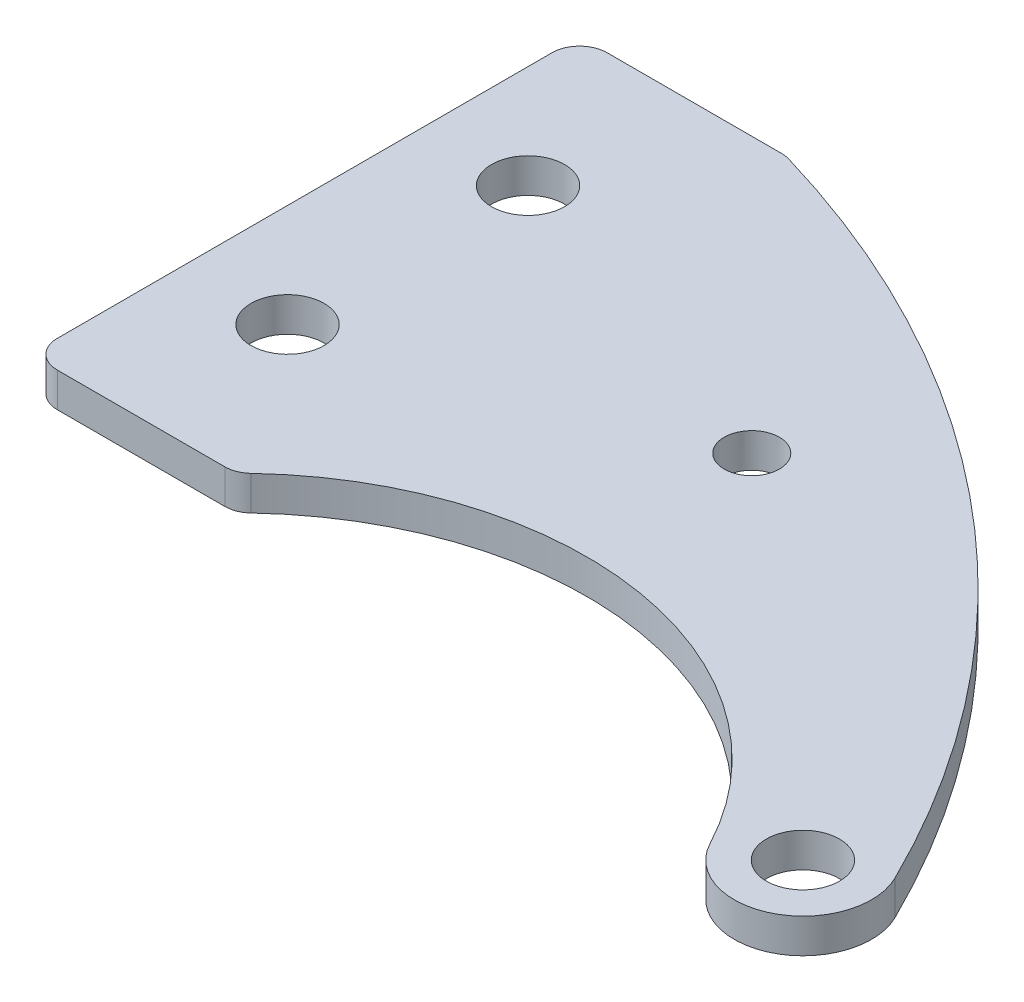
SolidWorks part; units mm, degrees
material "6061-T6 (SS)"
ref_plane "Front" through (0, 0, 0) normal (0, 0, 1) x (1, 0, 0)
ref_plane "Top" through (0, 0, 0) normal (0, 1, 0) x (1, 0, 0)
ref_plane "Right" through (0, 0, 0) normal (1, 0, 0) x (0, 0, -1)
sketch "Sketch1" plane through (0, 0, 0) normal (0, 1, 0) x (1, 0, 0)
  line L1 (0, 50.8) -> (19.05, 50.8)
  line L4 (0, 50.8) -> (0, 0)
  line L6 (0, 0) -> (19.05, 0)
  arc A0 (81.8992, -1.9621) -> (70.584, -7.7262) centre (76.2, -4.7625) cw
  arc A3 (19.05, 0) -> (70.584, -7.7262) centre (41.9743, -22.8241) cw
  arc A6 (81.8992, -1.9621) -> (19.05, 50.8) centre (-9.2873, -46.7682) ccw
  dimension "D1" = 19.05
  dimension "D2" = 4.7625
  dimension "D3" = 6.35
  dimension "D4" = 76.2
  dimension "D6" = 9.525
  dimension "D7" = 101.6
  dimension "D5" = 50.8
extrude "Boss-Extrude1" add sketch "Sketch1" along normal blind 3.175
hole_wizard "1/4 Clearance Hole2" positions "Sketch4" profile "Sketch3" hole size "1/4" standard "ANSI Inch" end condition through all
sketch "Sketch4" plane through (0, 0, 0) normal (0, -1, 0) x (-1, 0, 0)
  point P0 (-76.2, -4.7625)
sketch "Sketch3" plane through (76.2, 0, 4.7625) normal (1, 0, 0) x (0, 0, -1)
  line L0 (0, 0) -> (0, 3.175)
  line L1 (0, 3.175) -> (3.3782, 3.175)
  line L2 (3.3782, 3.175) -> (3.3782, 0)
  line L5 (3.3782, 0) -> (0, 0)
  line L11 (0, -6.35) -> (0, 107.95) construction
  dimension "Thru Hole Dia." = 6.7564
  dimension "Thru Hole Depth" = 3.175
hole_wizard "1/4 Clearance Hole1" positions "Sketch7" profile "Sketch8" hole size "1/4" standard "ANSI Inch" end condition through all
sketch "Sketch7" plane through (0, 3.175, 0) normal (0, 1, 0) x (1, 0, 0)
  line L9 (9.525, 0) -> (9.525, 14.2875) construction
  line L10 (0, 0) -> (19.05, 0) construction
  line L11 (9.525, 14.2875) -> (9.525, 36.5125) construction
  line L12 (9.525, 36.5125) -> (9.525, 50.8) construction
  line L13 (19.05, 50.8) -> (0, 50.8) construction
  point P0 (9.525, 36.5125)
  point P2 (9.525, 14.2875)
  dimension "D1" = 22.225
sketch "Sketch8" plane through (9.525, 3.175, -36.5125) normal (1, 0, 0) x (0, 0, 1)
  line L0 (0, 0) -> (0, 3.175)
  line L1 (0, 3.175) -> (3.3782, 3.175)
  line L2 (3.3782, 3.175) -> (3.3782, 0)
  line L5 (3.3782, 0) -> (0, 0)
  line L11 (0, -6.35) -> (0, 107.95) construction
  dimension "Thru Hole Dia." = 6.7564
  dimension "Thru Hole Depth" = 3.175
fillet "Fillet1" radius 2.54 4 edges at (19.05, 1.5875, 0) (0, 1.5875, 0) (0, 1.5875, -50.8) (19.05, 1.5875, -50.8)
sketch "Sketch11" plane through (0, 3.175, 0) normal (0, 1, 0) x (1, 0, 0)
  line L0 (41.275, 41.3568) -> (41.275, 9.5174) construction
  circle A0 centre (9.525, 36.5125) radius 3.3782 construction
  arc A1 (81.8992, -1.9621) -> (19.4036, 50.6966) centre (-9.2873, -46.7682) ccw construction
  arc A2 (70.584, -7.7262) -> (19.762, 0.6934) centre (41.9743, -22.8241) ccw construction
  point P0 (41.275, 25.4371)
  point P14 (0, 0)
  dimension "D1" = 31.75
hole_wizard "#10 Clearance Hole1" positions "Sketch11" profile "Sketch10" hole size "#10" standard "ANSI Inch" end condition up to next
sketch "Sketch10" plane through (41.275, 3.175, -25.4371) normal (1, 0, 0) x (0, 0, 1)
  line L0 (0, 0) -> (0, 3.175)
  line L1 (0, 3.175) -> (2.5527, 3.175)
  line L2 (2.5527, 3.175) -> (2.5527, 0)
  line L5 (2.5527, 0) -> (0, 0)
  line L11 (0, -6.35) -> (0, 107.95) construction
  dimension "Thru Hole Dia." = 5.1054
  dimension "Thru Hole Depth" = 3.175
